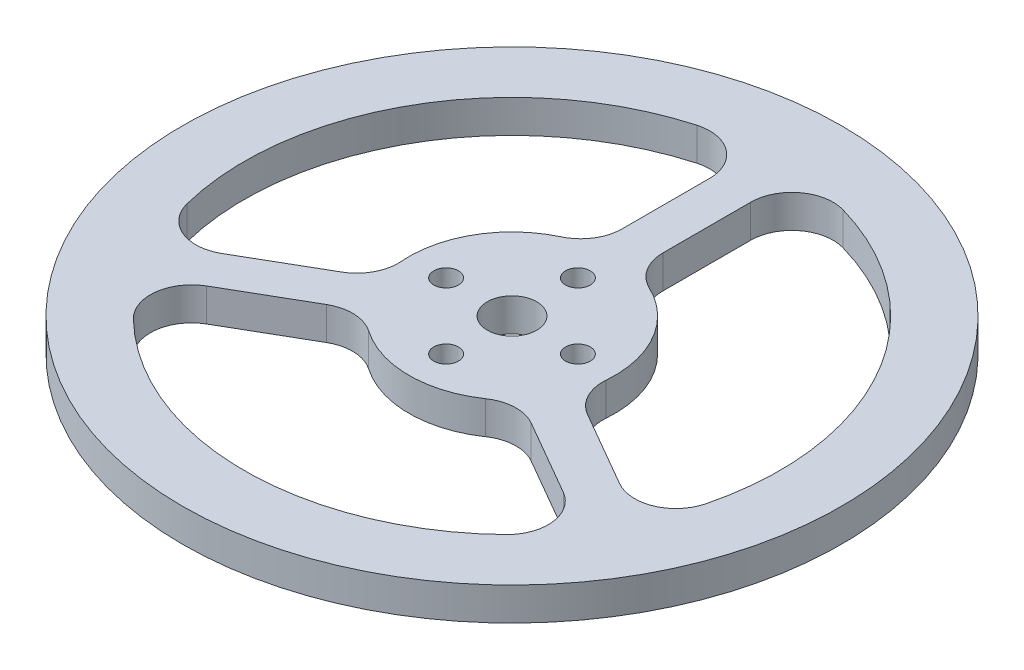
SolidWorks part; units mm, degrees
ref_plane "前视基准面" through (0, 0, 0) normal (0, 0, 1) x (1, 0, 0)
ref_plane "上视基准面" through (0, 0, 0) normal (0, 1, 0) x (1, 0, 0)
ref_plane "右视基准面" through (0, 0, 0) normal (1, 0, 0) x (0, 0, -1)
sketch "草图1" plane through (0, 0, 0) normal (0, 1, 0) x (1, 0, 0)
  circle A0 centre (0, 0) radius 40
  dimension "D1" = 80
extrude "凸台-拉伸1" add sketch "草图1" along normal blind 4
sketch "草图2" plane through (0, 4, 0) normal (0, 1, 0) x (1, 0, 0)
  circle A0 centre (8, 0) radius 1.5
  circle A1 centre (0, 8) radius 1.5
  circle A2 centre (-8, 0) radius 1.5
  circle A3 centre (0, -8) radius 1.5
  circle A4 centre (0, 0) radius 3
  dimension "D1" = 3
  dimension "D2" = 3
  dimension "D3" = 3
  dimension "D4" = 3
  dimension "D5" = 16
  dimension "D6" = 8
  dimension "D7" = 8
  dimension "D8" = 16
  dimension "D9" = 6
  dimension "D10" = 8
  dimension "D11" = 8
  dimension "D12" = 8
  dimension "D13" = 8
extrude "切除-拉伸1" cut sketch "草图2" against normal through all
sketch "草图3" plane through (0, 4, 0) normal (0, 1, 0) x (1, 0, 0)
  line L0 (3.0662, -4.6891) -> (29.047, -19.6891)
  line L1 (2.5278, 5) -> (-2.4722, 5)
  line L2 (2.5278, 5) -> (2.5278, 35)
  line L3 (2.5278, 35) -> (-2.4722, 35)
  line L4 (-2.4722, 5) -> (-2.4722, 35)
  line L5 (2.5278, 5) -> (-2.4722, 35) construction
  line L6 (2.5278, 35) -> (-2.4722, 5) construction
  line L7 (5.5662, -0.359) -> (31.547, -15.359)
  line L8 (29.047, -19.6891) -> (31.547, -15.359)
  line L9 (3.0662, -4.6891) -> (5.5662, -0.359)
  line L10 (-5.594, -0.3109) -> (-31.5748, -15.3109)
  line L11 (-3.094, -4.641) -> (-29.0748, -19.641)
  line L12 (-31.5748, -15.3109) -> (-29.0748, -19.641)
  line L13 (-5.594, -0.3109) -> (-3.094, -4.641)
  circle A0 centre (0, 0) radius 32.5
  circle A1 centre (0, 0) radius 12.5
  point P4 (0.0278, 20)
  point P19 (0, 0)
  dimension "D1" = 65
  dimension "D2" = 25
  dimension "D3" = 5
  dimension "D4" = 20
  dimension "D5" = 30
  dimension "D6" = 3
extrude "切除-拉伸2" cut sketch "草图3" against normal blind 10 contours A1 L4 A0 L10 | A1 L7 A0 L2 | A1 L11 A0 L0
fillet "圆角1" radius 5 12 edges at (9.3378, 2, 8.31) (-9.3754, 2, 8.2675) (-29.3245, 2, 14.0116) (-2.4722, 2, -32.4058) (-2.4722, 2, -12.2531) (-11.8656, 2, 3.9317) (26.7967, 2, 18.3899) (29.3004, 2, 14.0619) (-26.8282, 2, 18.3439) (11.8476, 2, 3.9856) (2.5278, 2, -12.2417) (2.5278, 2, -32.4015)
